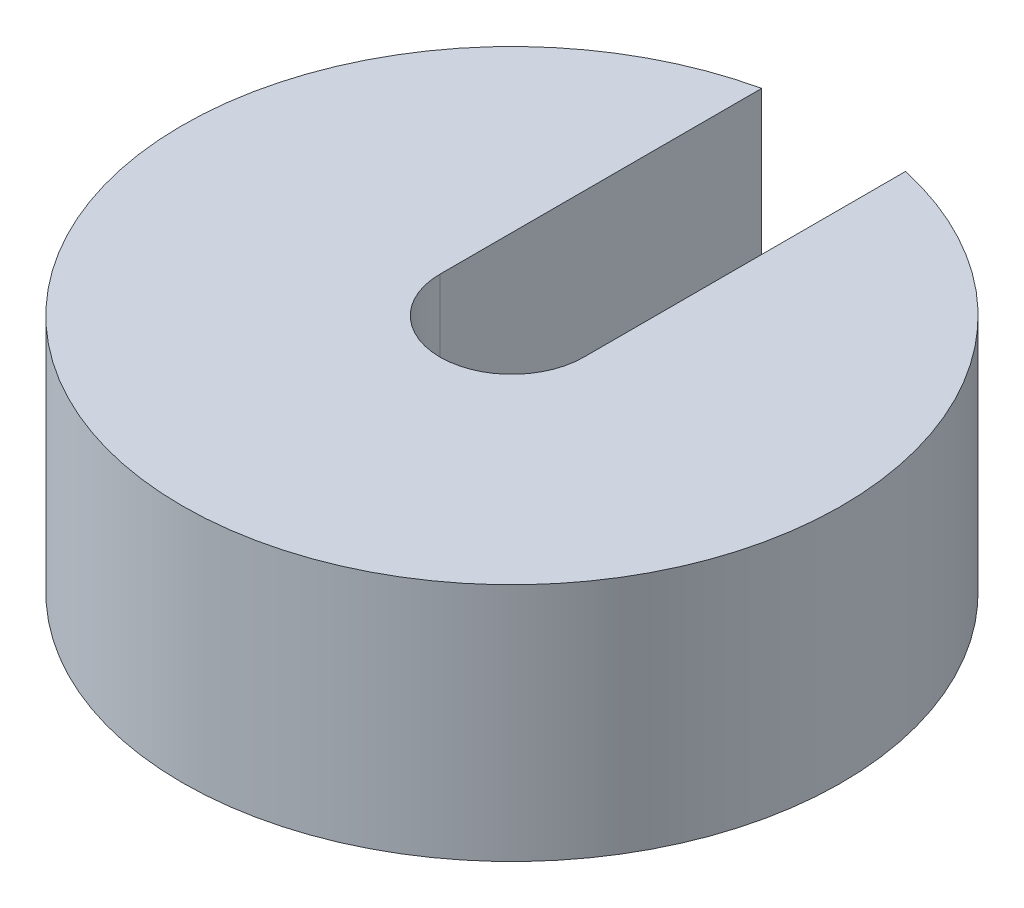
SolidWorks part; units mm, degrees
ref_plane "Front Plane" through (0, 0, 0) normal (0, 0, 1) x (1, 0, 0)
ref_plane "Top Plane" through (0, 0, 0) normal (0, 1, 0) x (1, 0, 0)
ref_plane "Right Plane" through (0, 0, 0) normal (1, 0, 0) x (0, 0, -1)
sketch "Sketch2" plane through (0, 0, 0) normal (0, 1, 0) x (1, 0, 0)
  line L0 (-6, 0) -> (-6, 26.8375)
  line L1 (6, 0) -> (6, 26.8375)
  circle A0 centre (0, 0) radius 27.5
  circle A1 centre (0, 0) radius 6
  dimension "D1" = 55
  dimension "D2" = 12
extrude "Boss-Extrude1" add sketch "Sketch2" along normal blind 20 contours A1 L0 A0 L1
